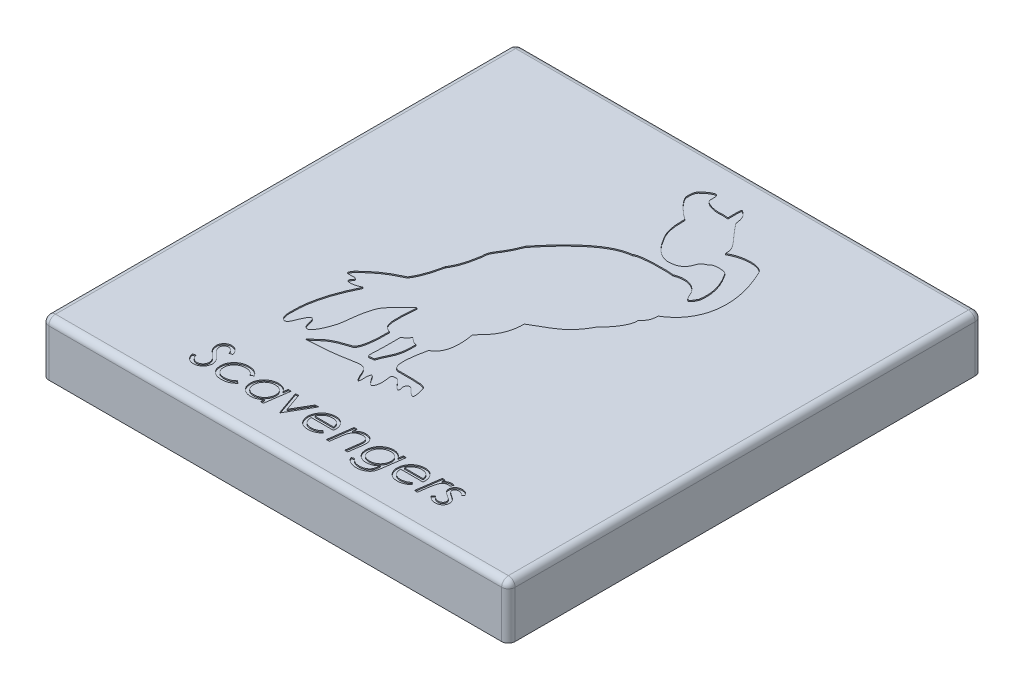
SolidWorks part; units mm, degrees
ref_plane "Plan de face" through (0, 0, 0) normal (0, 0, 1) x (1, 0, 0)
ref_plane "Plan de dessus" through (0, 0, 0) normal (0, 1, 0) x (1, 0, 0)
ref_plane "Plan de droite" through (0, 0, 0) normal (1, 0, 0) x (0, 0, -1)
sketch "Esquisse1" plane through (0, 0, 0) normal (0, 1, 0) x (1, 0, 0)
  line L1 (-103.5, -105.1) -> (103.5, -105.1)
  line L2 (-103.5, -105.1) -> (-103.5, 105.1)
  line L3 (-103.5, 105.1) -> (103.5, 105.1)
  line L4 (103.5, -105.1) -> (103.5, 105.1)
  line L5 (-103.5, -105.1) -> (103.5, 105.1) construction
  line L6 (-103.5, 105.1) -> (103.5, -105.1) construction
  point P0 (0, 0)
  dimension "D1" = 210.2
  dimension "D2" = 207
extrude "Boss.-Extru.1" add sketch "Esquisse1" along normal blind 23.86
shell "Coque1" thickness 5
fillet "Congé1" radius 3 8 edges at (0, 23.86, 105.1) (-103.5, 23.86, 0) (0, 23.86, -105.1) (103.5, 23.86, 0) (-103.5, 11.93, -105.1) (103.5, 11.93, -105.1) (103.5, 11.93, 105.1) (-103.5, 11.93, 105.1)
sketch "Esquisse3" plane through (0, 23.86, 0) normal (0, 1, 0) x (1, 0, 0)
  line L0 (-121.7874, 152.7633) -> (102.7373, 152.7633) construction
  spline S57 degree 3 poles (24.8823, 69.9401) (31.1637, 73.4173) (38.5784, 72.7835) (39.7561, 69.6709) knots 0 0 0 0 1 1 1 1
  spline S58 degree 3 poles (9.5801, -48.8957) (11.6759, -55.5777) (10.8079, -55.8563) (7.0355, -51.8249) knots 0 0 0 0 1 1 1 1
  spline S59 degree 3 poles (0.3604, -51.1329) (-4.0069, -50.6636) (-1.0802, -52.7172) (-1.9899, -57.6813) knots 0 0 0 0 1 1 1 1
  spline S60 degree 3 poles (-36.6828, -9.6145) (-34.8147, -6.4265) (-33.822, -4.3626) (-32.2024, 2.7783) knots 0 0 0 0 1 1 1 1
  spline S61 degree 3 poles (11.6653, 84.3339) (11.6653, 88.3751) (11.5462, 90.4467) (12.1696, 90.0537) knots 0 0 0 0 1 1 1 1
  spline S62 degree 3 poles (31.1733, 24.7337) (31.7137, 21.9255) (28.3562, 16.3954) (24.8823, 13.5775) knots 0 0 0 0 1 1 1 1
  spline S63 degree 3 poles (-8.8181, -33.7664) (-9.462, -33.9959) (-10.9407, -32.9668) (-12.1982, -31.8236) knots 0 0 0 0 1 1 1 1
  spline S64 degree 3 poles (21.4253, 50.1108) (26.2139, 52.0154) (31.3348, 50.6005) (33.0489, 45.5397) knots 0 0 0 0 1 1 1 1
  spline S65 degree 3 poles (0.3604, 90.3729) (1.4858, 89.8036) (0.3804, 86.6442) (1.2953, 86.2249) knots 0 0 0 0 1 1 1 1
  spline S66 degree 3 poles (-3.7446, -33.2462) (-5.523, -41.4873) (-5.9602, -47.4696) (-2.7527, -47.709) knots 0 0 0 0 1 1 1 1
  spline S67 degree 3 poles (-22.2825, 28.3615) (-12.4531, 40.4675) (-3.6843, 48.0555) (4.6389, 48.8886) knots 0 0 0 0 1 1 1 1
  spline S68 degree 3 poles (36.5752, 46.4539) (37.4114, 51.4434) (36.2795, 56.5622) (32.5397, 61.9422) knots 0 0 0 0 1 1 1 1
  spline S69 degree 3 poles (2.694, 74.0455) (-0.7121, 76.2877) (-6.0574, 81.4502) (-5.7111, 83.6722) knots 0 0 0 0 1 1 1 1
  spline S70 degree 3 poles (4.6389, -53.2452) (5.5608, -56.6438) (4.2926, -55.6753) (0.3604, -51.1329) knots 0 0 0 0 1 1 1 1
  spline S71 degree 3 poles (-32.2024, -31.8236) (-33.4466, -36.5872) (-33.222, -39.6246) (-34.071, -43.445) knots 0 0 0 0 1 1 1 1
  spline S72 degree 3 poles (-5.0879, -57.5774) (-6.7788, -54.5445) (-7.3317, -54.7038) (-7.4292, -57.8991) knots 0 0 0 0 1 1 1 1
  spline S73 degree 3 poles (-19.703, -34.7441) (-23.0752, -33.4911) (-23.7373, -31.8706) (-22.6866, -19.371) knots 0 0 0 0 1 1 1 1
  spline S74 degree 3 poles (-45.0348, -51.1329) (-46.6518, -56.167) (-49.7404, -53.5716) (-49.2553, -48.0536) knots 0 0 0 0 1 1 1 1
  spline S75 degree 3 poles (22.0992, 57.8328) (21.2005, 55.5612) (19.2507, 54.1257) (15.6691, 53.9385) knots 0 0 0 0 1 1 1 1
  spline S76 degree 3 poles (-33.1175, -56.1201) (-36.1537, -56.5119) (-35.9162, -56.1862) (-33.0881, -54.0927) knots 0 0 0 0 1 1 1 1
  spline S77 degree 3 poles (-22.6866, -19.371) (-31.2701, -27.6488) (-30.9608, -27.3503) (-32.2024, -31.8236) knots 0 0 0 0 1 1 1 1
  spline S78 degree 3 poles (4.6389, 48.8886) (6.3574, 50.4975) (18.4323, 50.5462) (21.4253, 50.1108) knots 0 0 0 0 1 1 1 1
  spline S79 degree 3 poles (25.3486, 61.6798) (23.8707, 60.391) (23.5595, 61.9142) (22.0992, 57.8328) knots 0 0 0 0 1 1 1 1
  spline S80 degree 3 poles (24.8823, 13.5775) (20.4803, 5.4707) (17.8213, 4.067) (7.3556, -1.8615) knots 0 0 0 0 1 1 1 1
  spline S81 degree 3 poles (-22.6866, -48.4806) (-20.9597, -48.2813) (-19.4895, -43.9984) (-19.703, -34.7441) knots 0 0 0 0 1 1 1 1
  spline S82 degree 3 poles (-34.071, -43.445) (-36.82, -52.3388) (-39.9289, -54.3922) (-40.9597, -48.8957) knots 0 0 0 0 1 1 1 1
  spline S83 degree 3 poles (5.114, 62.446) (3.3946, 65.3199) (2.647, 68.3182) (2.694, 74.0455) knots 0 0 0 0 1 1 1 1
  spline S84 degree 3 poles (7.0355, -51.8249) (6.2468, -50.9599) (4.6389, -51.1743) (4.6389, -53.2452) knots 0 0 0 0 1 1 1 1
  spline S85 degree 3 poles (-32.2024, 2.7783) (-31.0998, 4.621) (-29.4416, 7.0659) (-28.2331, 14.8214) knots 0 0 0 0 1 1 1 1
  spline S86 degree 2 poles (-5.7111, 83.6722) (-5.7467, 87.0201) (-4.5302, 87.7804) knots 0 0 0 1 1 1
  spline S87 degree 3 poles (12.1696, 90.0537) (14.575, 88.4915) (15.1554, 87.2866) (15.6691, 83.6722) knots 0 0 0 0 1 1 1 1
  spline S88 degree 3 poles (-9.4416, -57.8917) (-11.1857, -53.1256) (-12.7241, -53.4338) (-17.1025, -54.2757) knots 0 0 0 0 1 1 1 1
  spline S89 degree 3 poles (-47.9496, -22.837) (-46.9342, -21.6157) (-49.932, -21.4728) (-52.8401, -22.0719) (-50.656, -19.1901) knots 0 0 0 0 0.389407 1 1 1 1
  spline S90 degree 3 poles (-4.5302, 87.7804) (-2.2049, 90.0294) (-0.2625, 90.9064) (0.3604, 90.3729) knots 0 0 0 0 1 1 1 1
  spline S91 degree 3 poles (34.0135, 30.889) (33.8008, 27.1957) (32.9683, 26.5288) (31.1733, 24.7337) knots 0 0 0 0 1 1 1 1
  spline S92 degree 3 poles (-7.4292, -57.8991) (-7.2931, -61.5446) (-7.7155, -61.4315) (-9.4416, -57.8917) knots 0 0 0 0 1 1 1 1
  spline S93 degree 3 poles (-28.2331, 14.8214) (-28.3954, 19.3564) (-25.7244, 19.2113) (-22.2825, 28.3615) knots 0 0 0 0 1 1 1 1
  spline S94 degree 3 poles (8.0053, 84.2424) (10.0637, 84.5855) (11.7415, 83.9018) (11.6653, 84.3339) knots 0 0 0 0 1 1 1 1
  spline S95 degree 3 poles (0, -17.4818) (1.6103, -26.6119) (-0.0521, -31.3638) (-3.7446, -33.2462) knots 0 0 0 0 1 1 1 1
  spline S96 degree 3 poles (-12.1982, -31.8236) (-13.2558, -33.2529) (-13.5007, -33.5719) (-14.9926, -34.4362) knots 0 0 0 0 1 1 1 1
  spline S97 degree 3 poles (33.0489, 45.5397) (34.1916, 43.1454) (34.8397, 42.9211) (36.5752, 46.4539) knots 0 0 0 0 1 1 1 1
  spline S98 degree 3 poles (-2.7527, -47.709) (6.415, -47.5884) (8.5447, -47.7494) (9.5801, -48.8957) knots 0 0 0 0 1 1 1 1
  spline S99 degree 3 poles (-1.9899, -57.6813) (-2.6093, -60.0893) (-3.0695, -59.8749) (-5.0879, -57.5774) knots 0 0 0 0 1 1 1 1
  spline S100 degree 2 poles (-40.9597, -48.8957) (-42.0511, -43.4776) (-45.0348, -51.1329) knots 0 0 0 1 1 1
  spline S101 degree 3 poles (1.2953, 86.2249) (2.3882, 84.8017) (6.2901, 84.0518) (8.0053, 84.2424) knots 0 0 0 0 1 1 1 1
  spline S102 degree 3 poles (39.7561, 69.6709) (48.5503, 51.3114) (44.9086, 37.3313) (34.0135, 30.889) knots 0 0 0 0 1 1 1 1
  spline S103 degree 3 poles (-17.1025, -54.2757) (-21.8292, -55.2005) (-24.6333, -55.6059) (-33.1175, -56.1201) knots 0 0 0 0 1 1 1 1
  spline S104 degree 3 poles (-50.656, -19.1901) (-45.4198, -14.3254) (-43.2019, -12.6718) (-36.6828, -9.6145) knots 0 0 0 0 1 1 1 1
  spline S105 degree 3 poles (7.3556, -1.8615) (7.2799, -8.8245) (4.9798, -12.7363) (0, -17.4818) knots 0 0 0 0 1 1 1 1
  spline S106 degree 3 poles (-33.0881, -54.0927) (-30.3703, -51.2524) (-28.0489, -50.2068) (-22.6866, -48.4806) knots 0 0 0 0 1 1 1 1
  spline S107 degree 3 poles (-49.2553, -48.0536) (-49.3655, -41.4188) (-47.4874, -33.313) (-42.6089, -23.556) knots 0 0 0 0 1 1 1 1
  spline S108 degree 3 poles (-14.9926, -34.4362) (-14.6286, -51.1832) (-16.7766, -48.8736) (-12.517, -48.4806) knots 0 0 0 0 1 1 1 1
  spline S109 degree 3 poles (-42.6089, -23.556) (-47.1103, -25.4793) (-49.8764, -24.9218) (-47.9496, -22.837) knots 0 0 0 0 1 1 1 1
  spline S110 degree 2 poles (15.6691, 53.9385) (9.927, 53.8636) (5.114, 62.446) knots 0 0 0 1 1 1
  spline S111 degree 3 poles (15.6691, 83.6722) (22.4784, 74.9225) (24.7457, 74.7706) (24.8823, 69.9401) knots 0 0 0 0 1 1 1 1
  spline S112 degree 3 poles (-12.517, -48.4806) (-11.0243, -43.1943) (-8.5996, -43.0862) (-8.8181, -33.7664) knots 0 0 0 0 1 1 1 1
  spline S113 degree 3 poles (32.5397, 61.9422) (31.8457, 63.0768) (26.6467, 63.3931) (25.3486, 61.6798) knots 0 0 0 0 1 1 1 1
  text T0 "<i>Scavengers</i>" font "Century Gothic" height in points 56
extrude "Enlèv. mat.-Extru.1" cut sketch "Esquisse3" against normal blind 0.5
